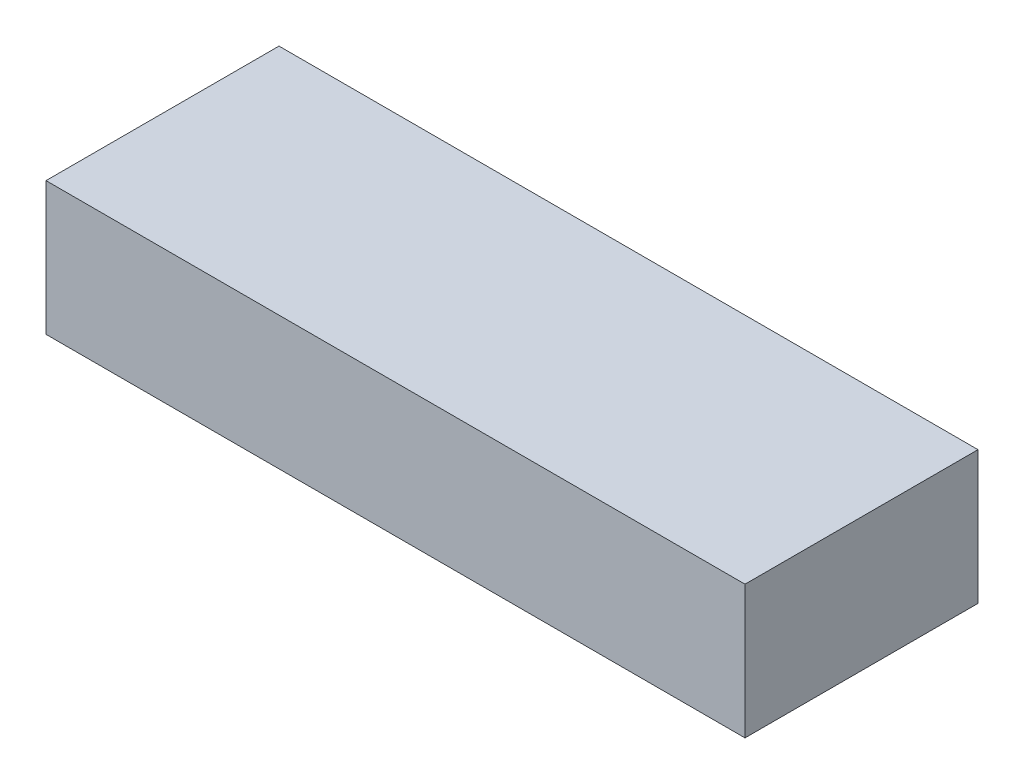
SolidWorks part; units mm, degrees
ref_plane "Front Plane" through (0, 0, 0) normal (0, 0, 1) x (1, 0, 0)
ref_plane "Top Plane" through (0, 0, 0) normal (0, 1, 0) x (1, 0, 0)
ref_plane "Right Plane" through (0, 0, 0) normal (1, 0, 0) x (0, 0, -1)
sketch "Sketch1" plane through (0, 0, 0) normal (0, 1, 0) x (1, 0, 0)
  line L1 (-47.1429, 16.5) -> (57.8571, 16.5)
  line L2 (-47.1429, 16.5) -> (-47.1429, -18.5)
  line L3 (-47.1429, -18.5) -> (57.8571, -18.5)
  line L4 (57.8571, 16.5) -> (57.8571, -18.5)
  dimension "D1" = 35
  dimension "D2" = 105
extrude "Boss-Extrude1" add sketch "Sketch1" along normal blind 20
